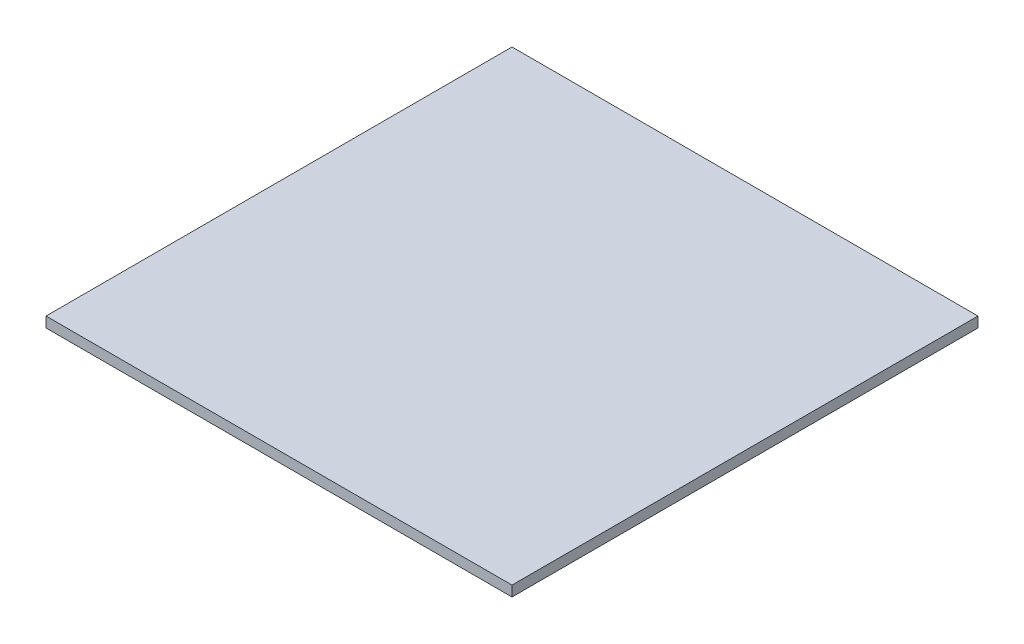
SolidWorks part; units mm, degrees
ref_plane "Front Plane" through (0, 0, 0) normal (0, 0, 1) x (1, 0, 0)
ref_plane "Top Plane" through (0, 0, 0) normal (0, 1, 0) x (1, 0, 0)
ref_plane "Right Plane" through (0, 0, 0) normal (1, 0, 0) x (0, 0, -1)
sketch "Sketch1" plane through (0, 0, 0) normal (0, 1, 0) x (1, 0, 0)
  line L1 (-225, -225) -> (225, -225)
  line L2 (-225, -225) -> (-225, 225)
  line L3 (-225, 225) -> (225, 225)
  line L4 (225, -225) -> (225, 225)
  line L5 (-225, -225) -> (225, 225) construction
  line L6 (-225, 225) -> (225, -225) construction
  point P0 (0, 0)
  dimension "D1" = 450
  dimension "D2" = 450
extrude "Boss-Extrude1" add sketch "Sketch1" along normal blind 10
